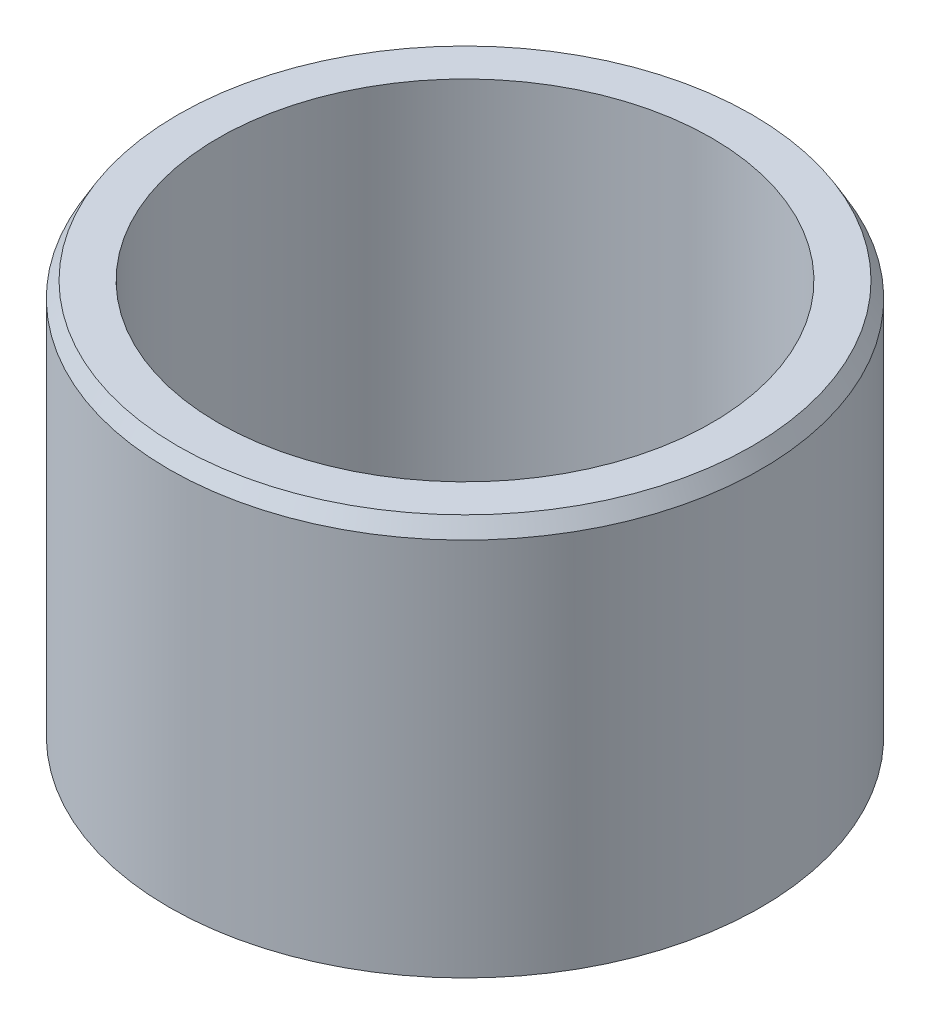
SolidWorks part; units mm, degrees
ref_plane "Front Plane" through (0, 0, 0) normal (0, 0, 1) x (1, 0, 0)
ref_plane "Top Plane" through (0, 0, 0) normal (0, 1, 0) x (1, 0, 0)
ref_plane "Right Plane" through (0, 0, 0) normal (1, 0, 0) x (0, 0, -1)
sketch "Sketch1" plane through (0, 0, 0) normal (0, 0, 1) x (1, 0, 0)
  line L0 (0, 21.4399) -> (0, -31.7069) construction
  line L2 (7.9375, 12.7) -> (9.525, 12.7)
  line L3 (7.9375, 12.7) -> (7.9375, 0)
  line L4 (7.9375, 0) -> (9.525, 0)
  line L5 (9.525, 12.7) -> (9.525, 0)
  dimension "D1" = 15.875
  dimension "D2" = 19.05
  dimension "D3" = 12.7
revolve "Revolve1" add sketch "Sketch1" angle 360 about L0
chamfer "Chamfer1" distance 0.5004 angle 30 1 edges at (0, 12.7, 9.525)
